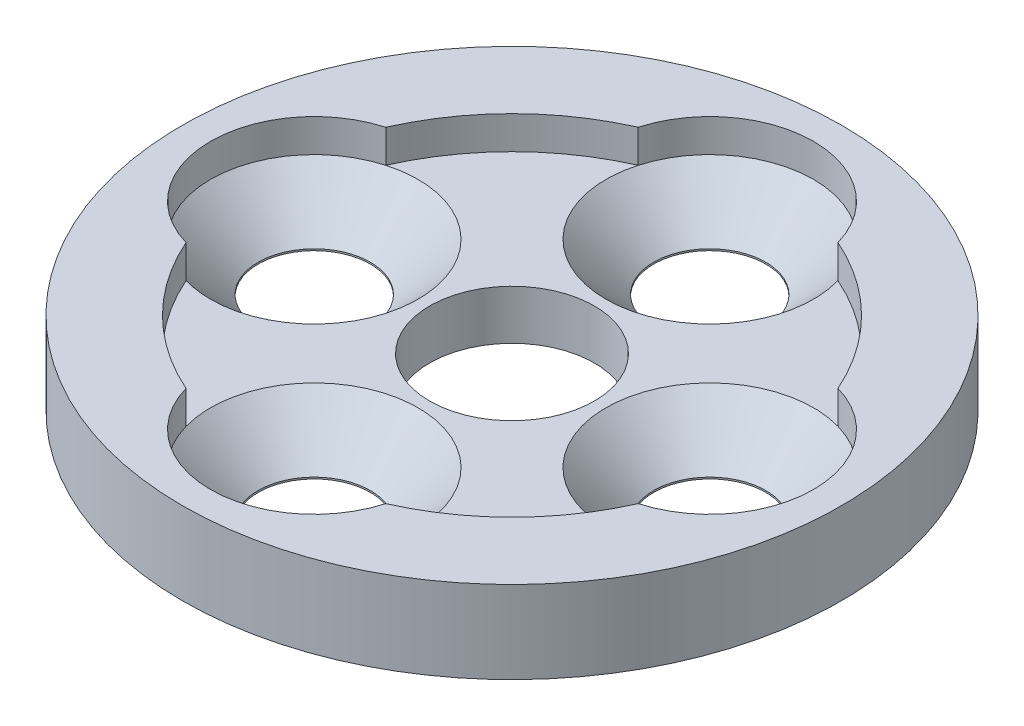
SolidWorks part; units mm, degrees
material "ABS"
ref_plane "Front Plane" through (0, 0, 0) normal (0, 0, 1) x (1, 0, 0)
ref_plane "Top Plane" through (0, 0, 0) normal (0, 1, 0) x (1, 0, 0)
ref_plane "Right Plane" through (0, 0, 0) normal (1, 0, 0) x (0, 0, -1)
sketch "Sketch1" plane through (0, 0, 0) normal (0, 1, 0) x (1, 0, 0)
  circle A0 centre (0, 0) radius 10
  dimension "D1" = 20
extrude "Boss-Extrude1" add sketch "Sketch1" along normal blind 1.5
sketch "Sketch2" plane through (0, 1.5, 0) normal (0, 1, 0) x (1, 0, 0)
  circle A0 centre (0, 0) radius 7.5
  circle A1 centre (0, 0) radius 10
  circle A2 centre (0, 0) radius 10 construction
  dimension "D1" = 15
extrude "Boss-Extrude2" add sketch "Sketch2" along normal blind 1
sketch "Sketch3" plane through (0, 1.5, 0) normal (0, 1, 0) x (1, 0, 0)
  circle A0 centre (0, 0) radius 6 construction
  circle A1 centre (0, 0) radius 7.5 construction
  point P2 (0, -6)
  point P3 (6, 0)
  point P6 (0, 6)
  point P7 (-6, 0)
  dimension "D1" = 12
hole_wizard "CSK for M3 Countersunk Flat Head Screw1" positions "3DSketch1" profile "Sketch4" countersink size "M3" standard "ISO" end condition up to next
sketch3d "3DSketch1"
  point P0 (-6, 1.5, 0)
  point P3 (0, 1.5, -6)
  point P6 (6, 1.5, 0)
  point P9 (0, 1.5, 6)
sketch "Sketch4" plane through (-6, 1.5, 0) normal (1, 0, 0) x (0, 0, 1)
  line L0 (0, 0) -> (0, 1.5)
  line L1 (0, 1.5) -> (1.7, 1.5)
  line L2 (1.7, 1.5) -> (1.7, 1.45)
  line L3 (1.7, 1.45) -> (3.15, 0)
  line L5 (3.15, 0) -> (0, 0)
  line L6 (-1.7, 1.45) -> (-3.15, 0) construction
  line L11 (0, -6.35) -> (0, 107.95) construction
  dimension "Thru Hole Dia." = 3.4
  dimension "Thru Hole Depth" = 1.5
  dimension "Near C'Sink Dia." = 6.3
  dimension "Near C'Sink Angle" = 90
sketch "Sketch5" plane through (0, 1.5, 0) normal (0, 1, 0) x (1, 0, 0)
  circle A0 centre (6, 0) radius 3.15
  circle A1 centre (0, -6) radius 3.15
  circle A2 centre (-6, 0) radius 3.15
  circle A3 centre (0, 6) radius 3.15
  arc A4 (6.8606, 3.0302) -> (6.8606, -3.0302) centre (6, 0) ccw construction
  arc A5 (3.0302, -6.8606) -> (-3.0302, -6.8606) centre (0, -6) ccw construction
  arc A6 (-6.8606, -3.0302) -> (-6.8606, 3.0302) centre (-6, 0) ccw construction
  arc A7 (-3.0302, 6.8606) -> (3.0302, 6.8606) centre (0, 6) ccw construction
extrude "Cut-Extrude1" cut sketch "Sketch5" along normal blind 21
sketch "Sketch6" plane through (0, 1.5, 0) normal (0, 1, 0) x (1, 0, 0)
  circle A0 centre (0, 0) radius 2.5
  dimension "D1" = 5
extrude "Cut-Extrude2" cut sketch "Sketch6" against normal through all both and the other way through all
